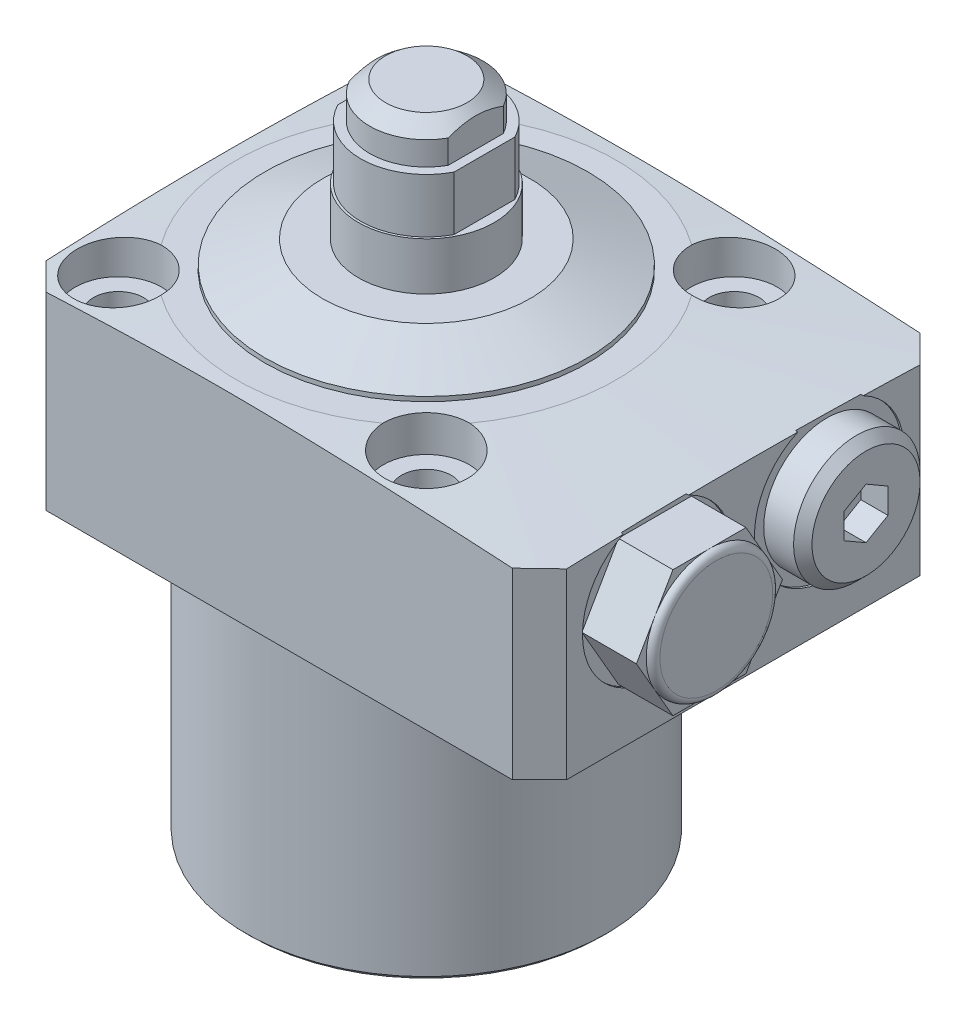
SolidWorks part; units mm, degrees
material "Alloy Steel"
ref_plane "Front Plane" through (0, 0, 0) normal (0, 0, 1) x (1, 0, 0)
ref_plane "Top Plane" through (0, 0, 0) normal (0, 1, 0) x (1, 0, 0)
ref_plane "Right Plane" through (0, 0, 0) normal (1, 0, 0) x (0, 0, -1)
sketch "Sketch1" plane through (0, 0, 0) normal (0, 0, 1) x (1, 0, 0)
  line L0 (0, 0) -> (0, -9.6761) construction
  line L1 (-19.925, 0) -> (-50, 0)
  line L2 (-50, 0) -> (-50, 19.4721)
  line L8 (-19.925, -32.5) -> (-19.925, 0)
  line L9 (-50, 19.4721) -> (-21, 21.5)
  line L10 (-21, 21.5) -> (0, 21.5)
  line L11 (0, 21.5) -> (0, -32.5)
  line L13 (-19.925, -32.5) -> (0, -32.5)
  dimension "D2" = 32.5
  dimension "D3" = 50
  dimension "D7" = 54
  dimension "D8" = 4
  dimension "D9" = 42
  dimension "D10" = 39.85
revolve "Revolve1" add sketch "Sketch1" angle 360 about L0
sketch "Sketch2" plane through (0, 21.5, 0) normal (0, 1, 0) x (1, 0, 0)
  line L0 (0, 0) -> (0, 57.0347) construction
  line L1 (-22.5, 22.5) -> (35, 22.5)
  line L2 (-22.5, 22.5) -> (-22.5, -22.5)
  line L3 (-22.5, -22.5) -> (35, -22.5)
  line L4 (35, 22.5) -> (35, -22.5)
  line L5 (0, 0) -> (-71.4399, 0) construction
  dimension "D1" = 45
  dimension "D2" = 22.5
  dimension "D3" = 57.5
extrude "Cut-Extrude1" cut sketch "Sketch2" against normal through all flip side to cut
chamfer "Chamfer2" distance 3 angle 45 4 edges at (-22.5, 10.3717, -22.5) (35, 10.0295, -22.5) (35, 10.0295, 22.5) (-22.5, 10.3717, 22.5)
sketch "Sketch4" plane through (0, 0, 0) normal (0, 0, 1) x (1, 0, 0)
  line L0 (0, 0) -> (0, 85.9979) construction
  line L1 (0, 39.75) -> (-6.25, 39.75)
  line L2 (-6.25, 39.75) -> (-6.25, 35.762)
  line L3 (-6.25, 35.762) -> (-7.25, 35.762)
  line L4 (-7.25, 35.762) -> (-7.25, 29.782)
  line L5 (-7.25, 29.782) -> (-7.5, 29.782)
  line L6 (-7.5, 29.782) -> (-7.5, 21.5)
  line L7 (21, 21.5) -> (-21, 21.5) construction
  line L8 (-7.5, 21.5) -> (0, 21.5)
  line L9 (0, 21.5) -> (0, 39.75)
  line L12 (32, 0) -> (-19.5, 0) construction
  dimension "D1" = 39.75
  dimension "D2" = 3.988
  dimension "D3" = 12.5
  dimension "D4" = 15
  dimension "D5" = 14.5
  dimension "D6" = 9.968
revolve "Revolve2" add sketch "Sketch4" angle 360 about L0
chamfer "Chamfer1" distance 1.3715 angle 51.98 1 edges at (0, 39.75, -6.25)
sketch "Sketch5" plane through (0, 0, 0) normal (0, 0, 1) x (1, 0, 0)
  line L0 (7.25, 35.762) -> (-7.25, 35.762) construction
  line L1 (-5.46, 35.762) -> (-7.25, 35.762)
  line L2 (-5.46, 35.762) -> (-5.46, 39.75)
  line L3 (-5.46, 39.75) -> (-7.25, 39.75)
  line L4 (-7.25, 35.762) -> (-7.25, 39.75)
  line L5 (4.4959, 39.75) -> (-4.4959, 39.75) construction
  line L6 (-7.25, 35.762) -> (-7.25, 29.782) construction
  line L7 (0, 0) -> (0, 109.405) construction
  line L8 (7.25, 35.762) -> (7.25, 39.75)
  line L9 (5.46, 39.75) -> (7.25, 39.75)
  line L10 (5.46, 35.762) -> (5.46, 39.75)
  line L11 (5.46, 35.762) -> (7.25, 35.762)
  dimension "D1" = 10.92
extrude "Cut-Extrude2" cut sketch "Sketch5" against normal through all and the other way through all
sketch "Sketch6" plane through (0, 0, 0) normal (0, 0, 1) x (1, 0, 0)
  line L0 (7.25, 35.762) -> (-7.25, 35.762) construction
  line L1 (-6.425, 35.762) -> (-7.5, 35.762)
  line L2 (-6.425, 35.762) -> (-6.425, 29.782)
  line L3 (-6.425, 29.782) -> (-7.5, 29.782)
  line L4 (-7.5, 35.762) -> (-7.5, 29.782)
  line L5 (0, 0) -> (0, 83.5625) construction
  line L6 (7.5, 35.762) -> (7.5, 29.782)
  line L7 (6.425, 29.782) -> (7.5, 29.782)
  line L8 (6.425, 35.762) -> (6.425, 29.782)
  line L9 (6.425, 35.762) -> (7.5, 35.762)
  dimension "D1" = 12.85
extrude "Cut-Extrude3" cut sketch "Sketch6" against normal through all and the other way through all
sketch "Sketch10" plane through (0, 21.5, 0) normal (0, 1, 0) x (1, 0, 0)
  line L0 (0, 0) -> (0, 37.6461) construction
  line L1 (0, 0) -> (33.5022, 0) construction
  circle A0 centre (-17, 17) radius 4.75
  dimension "D1" = 9.5
  dimension "D2" = 17
  dimension "D3" = 17
extrude "Cut-Extrude4" cut sketch "Sketch10" against normal offset from surface (4 mm away) 17.5 up to face at (0, 0, 19.925)
hole_wizard "Ø5.5 (5.5) Diameter Hole1" positions "3DSketch1" profile "Sketch11" hole size "Ø5.5" standard "Ansi Metric" end condition through all
sketch3d "3DSketch1"
  circle A0 centre (-17, 17.5, -17) radius 4.75 construction
  point P0 (-17, 17.5, -17)
  point P6 (-17, 22.25, -17)
sketch "Sketch11" plane through (-17, 17.5, -17) normal (1, 0, 0) x (0, 0, 1)
  line L0 (0, 0) -> (0, 50)
  line L1 (0, 50) -> (2.75, 50)
  line L2 (2.75, 50) -> (2.75, 0)
  line L5 (2.75, 0) -> (0, 0)
  line L11 (0, -6.35) -> (0, 107.95) construction
  dimension "Thru Hole Dia." = 5.5
  dimension "Thru Hole Depth" = 50
pattern_circular "CirPattern1" count 4 over 360 about axis through (0, 0, 0) along (0, 1, 0) of "Ø5.5 (5.5) Diameter Hole1", "Cut-Extrude4"
ref_plane "Plane1" through (0, 0, -9.5) normal (0, 0, 1) x (1, 0, 0)
sketch "Sketch12" plane through (0, 0, -9.5) normal (0, 0, 1) x (1, 0, 0)
  line L0 (17.9573, 13) -> (55.5469, 13) construction
  line L2 (35, 21.255) -> (34.75, 21.255)
  line L4 (34.75, 21.255) -> (34.75, 17.953)
  line L5 (34.75, 17.953) -> (34.2166, 17.4196)
  line L6 (34.2166, 17.4196) -> (24.1836, 17.4196)
  line L7 (24.1836, 17.4196) -> (21.528, 13)
  line L8 (21.528, 13) -> (35, 13)
  line L9 (35, 13) -> (35, 21.255)
  line L10 (35, 20.1668) -> (35, 0) construction
  line L11 (-19.925, -32.5) -> (19.925, -32.5) construction
  dimension "D1" = 45.5
  dimension "D2" = 16.51
  dimension "D3" = 0.25
  dimension "D4" = 8.8392
  dimension "D5" = 59
  dimension "D6" = 10.5664
  dimension "D7" = 45
  dimension "D8" = 0.5334
revolve "Cut-Revolve2" cut sketch "Sketch12" angle 360 about L0
sketch "Sketch13" plane through (0, 0, -9.5) normal (0, 0, 1) x (1, 0, 0)
  line L0 (10.4663, 13) -> (36.2703, 13) construction
  line L1 (34.2166, 13) -> (24.1836, 13) construction
  line L3 (34.75, 19.985) -> (38.045, 19.985)
  line L4 (34.75, 4.745) -> (34.75, 20.5019) construction
  line L5 (38.045, 19.985) -> (39.06, 18.97)
  line L6 (39.06, 18.97) -> (39.06, 13)
  line L7 (39.06, 13) -> (34.75, 13)
  line L8 (34.75, 13) -> (34.75, 19.985)
  dimension "D1" = 4.31
  dimension "D2" = 13.97
  dimension "D3" = 45
  dimension "D4" = 1.015
revolve "Revolve3" add sketch "Sketch13" angle 360 about L0
sketch "Sketch14" plane through (39.06, 0, 0) normal (1, 0, 0) x (0, 0, -1)
  line L1 (11.9255, 11.5996) -> (11.9255, 14.4004)
  line L2 (11.9255, 14.4004) -> (9.5, 15.8007)
  line L3 (9.5, 15.8007) -> (7.0745, 14.4004)
  line L4 (7.0745, 14.4004) -> (7.0745, 11.5996)
  line L5 (7.0745, 11.5996) -> (9.5, 10.1993)
  line L6 (9.5, 10.1993) -> (11.9255, 11.5996)
  circle A0 centre (9.5, 13) radius 2.4255 construction
  dimension "D1" = 4.851
extrude "Cut-Extrude5" cut sketch "Sketch14" against normal blind 3
sketch "Sketch16" plane through (9.5, 0, -9.5) normal (0, 0, -1) x (-1, 0, 0)
  line L0 (-17.5, -1.224) -> (-17.5, -24.6754) construction
  line L1 (-17.5, 13.5022) -> (-20, 12)
  line L2 (-20, 12) -> (-20, 2.875)
  line L3 (-20, 2.875) -> (-20.625, 2.25)
  line L4 (-20.625, 2.25) -> (-22.5, 2.25)
  line L5 (-22.5, 2.25) -> (-22.5, 0)
  line L7 (-22.5, 0) -> (-17.5, 0)
  line L8 (-17.5, 0) -> (-17.5, 13.5022)
  line L9 (9.5, -32.5) -> (9.5, 0) construction
  line L10 (29, 0) -> (-22.5, 0) construction
  dimension "D1" = 27
  dimension "D2" = 5
  dimension "D3" = 59
  dimension "D4" = 10
  dimension "D5" = 2.25
  dimension "D6" = 45
  dimension "D7" = 0.625
  dimension "D8" = 9.75
revolve "Cut-Revolve4" cut sketch "Sketch16" angle 360 about L0
pattern_linear "LPattern1" count 2 spacing 19 along (0, 0, 1) of "Cut-Extrude5", "Cut-Revolve2", "Cut-Revolve4"
sketch "Sketch18" plane through (-9.5, 0, -9.5) normal (0, 0, 1) x (1, 0, 0)
  line L0 (36.5, -2.5857) -> (36.5, -21.6782) construction
  line L3 (31.5, 2.25) -> (41.5, 2.25) construction
  line L4 (36.5, 2.875) -> (36.5, 8.5804) construction
  circle A0 centre (33.001, 0.75) radius 1.5
  dimension "D1" = 3
  dimension "D2" = 1.5
  dimension "D3" = 6.998
revolve "Revolve4" add sketch "Sketch18" angle 360 about L0
pattern_linear "LPattern2" count 2 spacing 19 along (0, 0, 1) of bodies 124
chamfer "Chamfer3" distance 0.5 angle 45 1 edges at (0, -32.5, 19.925)
fillet "Fillet1" radius 0.5 1 edges at (0, 0, 19.925)
ref_axis "Axis1" through (0, 29.782, 0) along (0, -1, 0)
sketch "Sketch19" plane through (0, 0, 0) normal (0, 0, 1) x (1, 0, 0)
  line L0 (7.5, 21.5) -> (17.82, 21.5)
  line L1 (21, 21.5) -> (17.0566, 21.5) construction
  line L2 (17.82, 21.5) -> (17.82, 22)
  line L3 (17.82, 22) -> (11.4734, 24.5)
  line L4 (11.4734, 24.5) -> (7.5, 24.5)
  line L5 (7.5, 21.5) -> (7.5, 29.782) construction
  line L6 (7.5, 24.5) -> (7.5, 21.5)
  line L7 (0, 29.782) -> (0, 21.5) construction
  dimension "D1" = 0.5
  dimension "D2" = 17.82
  dimension "D3" = 21.5
  dimension "D4" = 3
revolve "Revolve5" add sketch "Sketch19" angle 360 about axis through (0, 29.782, 0) along (0, -1, 0)
sketch "Sketch21" plane through (34.75, 0, 0) normal (1, 0, 0) x (0, 0, -1)
  line L1 (-1.4344, 13) -> (-5.4672, 19.985)
  line L2 (-5.4672, 19.985) -> (-13.5328, 19.985)
  line L3 (-13.5328, 19.985) -> (-17.5656, 13)
  line L4 (-17.5656, 13) -> (-13.5328, 6.015)
  line L5 (-13.5328, 6.015) -> (-5.4672, 6.015)
  line L6 (-5.4672, 6.015) -> (-1.4344, 13)
  circle A0 centre (-9.5, 13) radius 6.985 construction
  dimension "D1" = 13.97
extrude "Boss-Extrude1" add sketch "Sketch21" along normal blind 6.78
ref_plane "Plane2" through (0, 0, 9.5) normal (0, 0, -1) x (-1, 0, 0)
sketch "Sketch22" plane through (0, 0, 9.5) normal (0, 0, -1) x (-1, 0, 0)
  line L5 (-41.53, 19.223) -> (-44.7994, 19.223)
  line L6 (-40.768, 19.985) -> (-40.768, 22.7945)
  line L7 (-40.768, 22.7945) -> (-44.7994, 22.7945)
  line L8 (-44.7994, 19.223) -> (-44.7994, 22.7945)
  arc A0 (-41.53, 19.223) -> (-40.768, 19.985) centre (-40.768, 19.223) cw
revolve "Cut-Revolve5" cut sketch "Sketch22" angle 360 about axis through (17.9573, 13, 9.5) along (-1, 0, 0)
